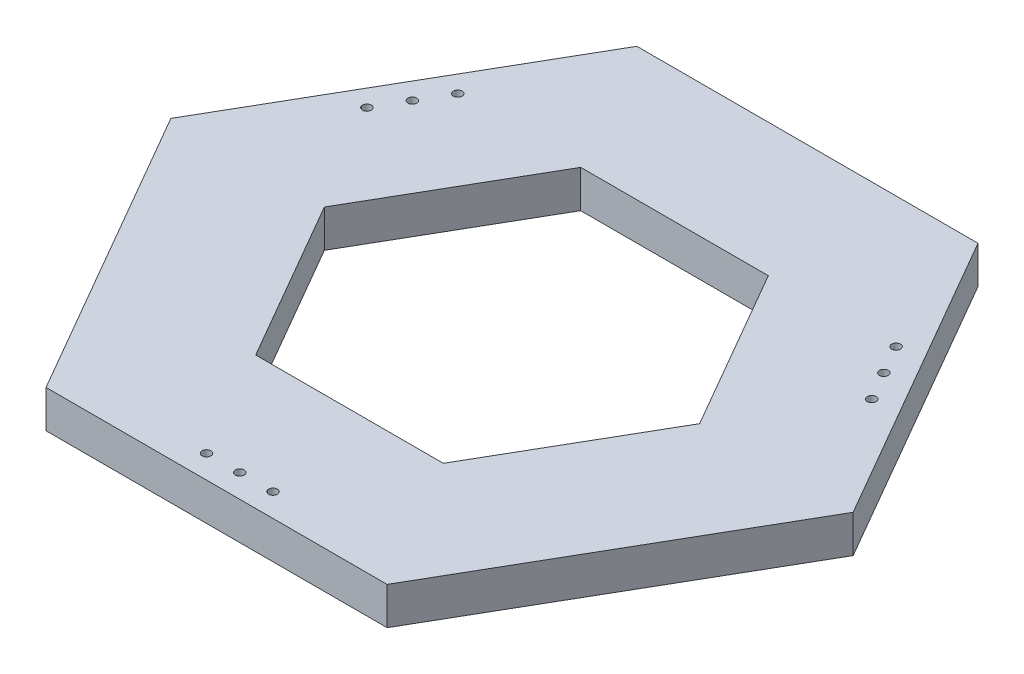
SolidWorks part; units mm, degrees
material "Pino"
ref_plane "Alzado" through (0, 0, 0) normal (0, 0, 1) x (1, 0, 0)
ref_plane "Planta" through (0, 0, 0) normal (0, 1, 0) x (1, 0, 0)
ref_plane "Vista lateral" through (0, 0, 0) normal (1, 0, 0) x (0, 0, -1)
sketch "Croquis1" plane through (0, 0, 0) normal (0, 1, 0) x (1, 0, 0)
  line L1 (115.4701, -200) -> (230.9401, 0)
  line L2 (230.9401, 0) -> (115.4701, 200)
  line L3 (115.4701, 200) -> (-115.4701, 200)
  line L4 (-115.4701, 200) -> (-230.9401, 0)
  line L5 (-230.9401, 0) -> (-115.4701, -200)
  line L6 (-115.4701, -200) -> (115.4701, -200)
  line L7 (127.0171, 0) -> (63.5085, 110)
  line L8 (63.5085, 110) -> (-63.5085, 110)
  line L9 (-63.5085, 110) -> (-127.0171, 0)
  line L10 (-127.0171, 0) -> (-63.5085, -110)
  line L11 (-63.5085, -110) -> (63.5085, -110)
  line L12 (63.5085, -110) -> (127.0171, 0)
  circle A0 centre (0, 0) radius 200 construction
  circle A1 centre (0, 0) radius 110 construction
  dimension "D1" = 400
  dimension "D2" = 90
extrude "Saliente-Extruir1" add sketch "Croquis1" along normal blind 25.4
sketch "Croquis2" plane through (0, 25.4, 0) normal (0, 1, 0) x (1, 0, 0)
  line L0 (-115.4701, -200) -> (115.4701, -200) construction
  circle A0 centre (0, -184.3) radius 3
  circle A1 centre (-22.5, -184.3) radius 3
  circle A2 centre (22.5, -184.3) radius 3
  circle A3 centre (-148.3585, 111.6356) radius 3
  circle A4 centre (-159.6085, 92.15) radius 3
  circle A5 centre (-170.8585, 72.6644) radius 3
  circle A6 centre (170.8585, 72.6644) radius 3
  circle A7 centre (159.6085, 92.15) radius 3
  circle A8 centre (148.3585, 111.6356) radius 3
  point P2 (0, -200)
  point P25 (0, 0)
  dimension "D2" = 6
  dimension "D1" = 15.7
  dimension "D3" = 22.5
  dimension "D4" = 22.5
  dimension "D5" = 115.4701
  dimension "D6" = 3
extrude "Cortar-Extruir2" cut sketch "Croquis2" against normal through all
